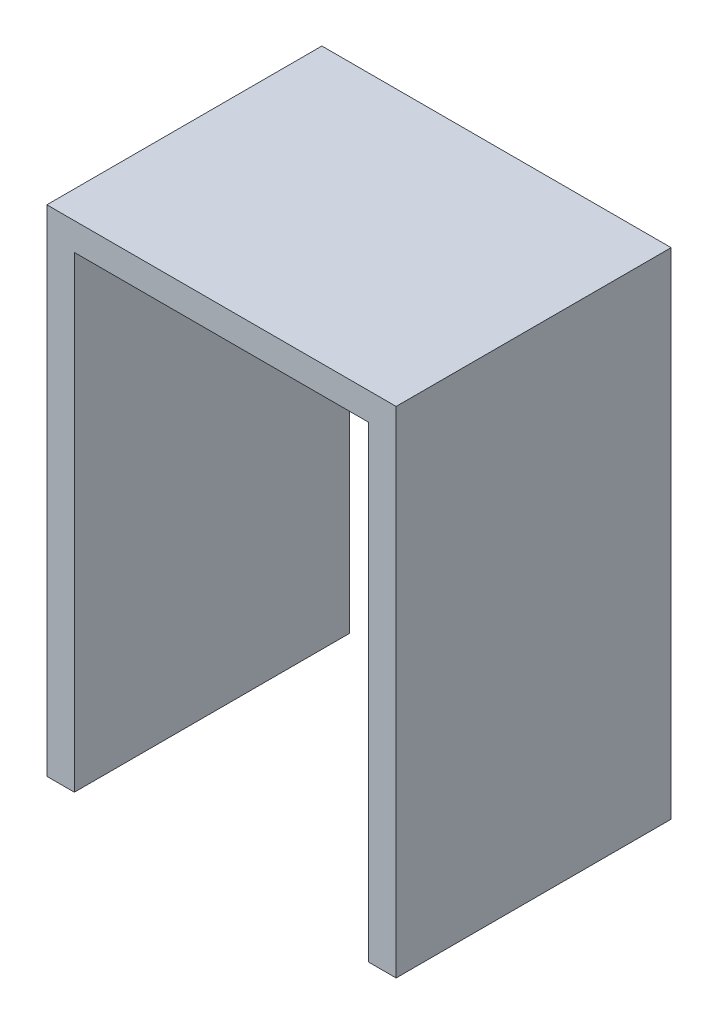
SolidWorks part; units mm, degrees
ref_plane "Front Plane" through (0, 0, 0) normal (0, 0, 1) x (1, 0, 0)
ref_plane "Top Plane" through (0, 0, 0) normal (0, 1, 0) x (1, 0, 0)
ref_plane "Right Plane" through (0, 0, 0) normal (1, 0, 0) x (0, 0, -1)
sketch "Sketch1" plane through (0, 0, 0) normal (0, 0, 1) x (1, 0, 0)
  line L0 (-2.3333, 0) -> (-2.3333, 17)
  line L1 (-2.3333, 17) -> (8.3667, 17)
  line L2 (8.3667, 17) -> (8.3667, 0)
  line L3 (8.3667, 0) -> (9.3667, 0)
  line L4 (9.3667, 0) -> (9.3667, 18)
  line L5 (9.3667, 18) -> (-3.3333, 18)
  line L6 (-3.3333, 18) -> (-3.3333, 0)
  line L7 (-3.3333, 0) -> (-2.3333, 0)
  dimension "D1" = 1
  dimension "D2" = 1
  dimension "D3" = 1
  dimension "D4" = 12.7
  dimension "D5" = 18
extrude "Boss-Extrude1" add sketch "Sketch1" along normal blind 10
